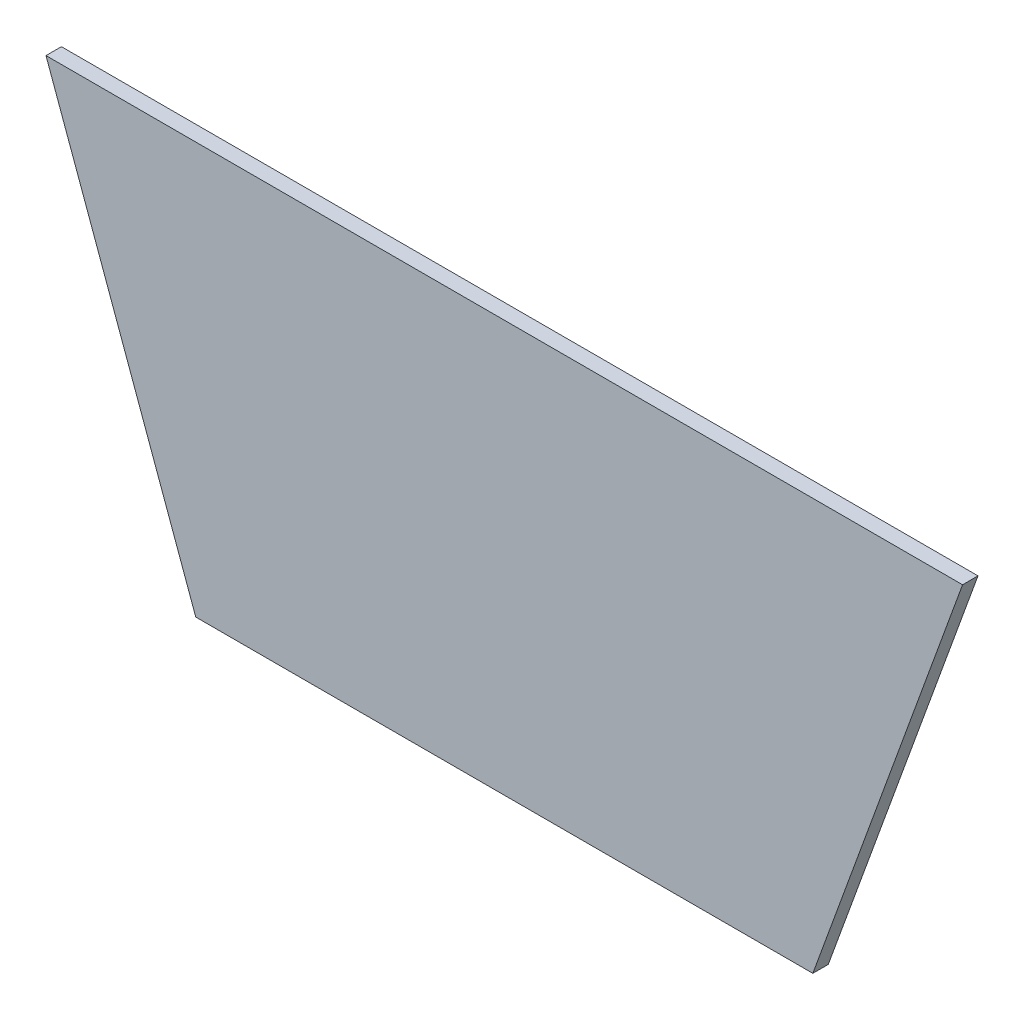
SolidWorks part; units mm, degrees
ref_plane "Plan de face" through (0, 0, 0) normal (0, 0, 1) x (1, 0, 0)
ref_plane "Plan de dessus" through (0, 0, 0) normal (0, 1, 0) x (1, 0, 0)
ref_plane "Plan de droite" through (0, 0, 0) normal (1, 0, 0) x (0, 0, -1)
sketch "Esquisse1" plane through (0, 0, 0) normal (0, 0, 1) x (1, 0, 0)
  line L0 (-60, -9) -> (-89.1176, 71)
  line L1 (-89.1176, 71) -> (89.1176, 71)
  line L2 (60, -9) -> (89.1176, 71)
  line L3 (0, -9) -> (0, 71) construction
  line L4 (-60, -9) -> (60, -9) construction
  line L5 (-60, -9) -> (60, -9)
  point P7 (-74.5588, 31)
  point P10 (0, 0)
  point P11 (-104.0057, 71)
  point P12 (0, 0)
  dimension "D1" = 80
  dimension "D2" = 110
extrude "Boss.-Extru.1" add sketch "Esquisse1" along normal blind 3
sketch "Esquisse2" plane through (-198.9411, -77.8877, -451.1056) normal (-0.8988, -0.2971, 0.3222) x (0.2886, 0.1521, 0.9453)
  line L0 (512.876, 25.911) -> (512.876, 147.228) construction
  point P2 (512.876, 25.911)
